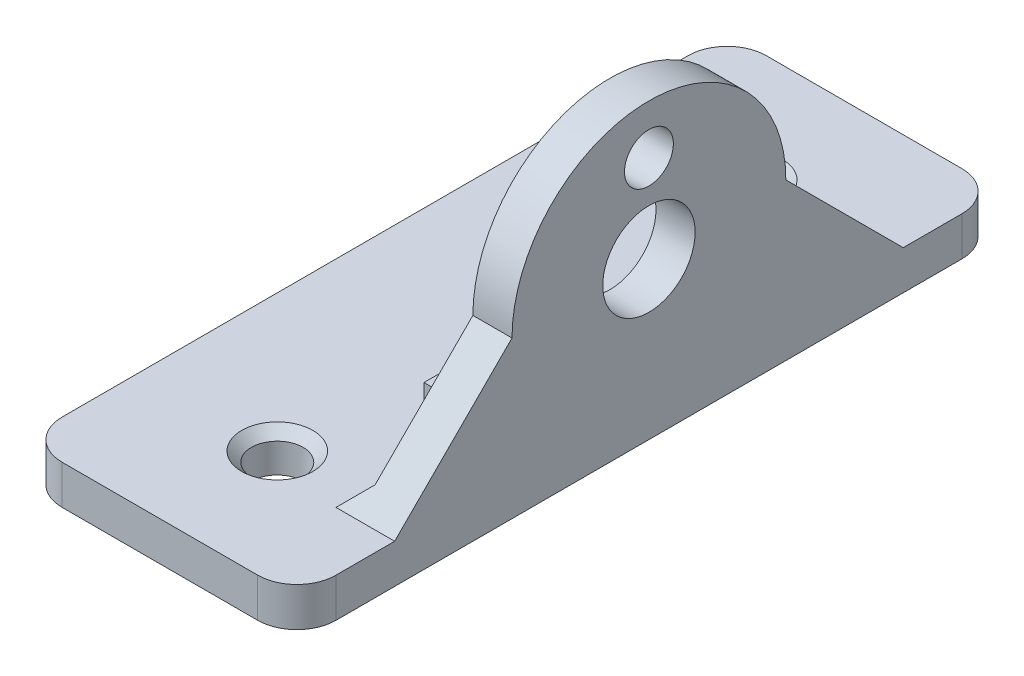
SolidWorks part; units mm, degrees
ref_plane "Front Plane" through (0, 0, 0) normal (0, 0, 1) x (1, 0, 0)
ref_plane "Top Plane" through (0, 0, 0) normal (0, 1, 0) x (1, 0, 0)
ref_plane "Right Plane" through (0, 0, 0) normal (1, 0, 0) x (0, 0, -1)
sketch "Sketch1" plane through (0, 0, 0) normal (1, 0, 0) x (0, 0, -1)
  line L0 (-28.575, 0) -> (28.575, 0)
  line L1 (28.575, 0) -> (28.575, 3.175)
  line L2 (28.575, 3.175) -> (20.6375, 3.175)
  line L3 (-20.6375, 3.175) -> (-28.575, 3.175)
  line L4 (-28.575, 3.175) -> (-28.575, 0)
  line L5 (20.6375, 3.175) -> (11.1125, 12.7)
  line L6 (0, 30.8716) -> (0, -13.4832) construction
  line L7 (-20.6375, 3.175) -> (-11.1125, 12.7)
  arc A0 (11.1125, 12.7) -> (-11.1125, 12.7) centre (0, 12.7) ccw
  circle A1 centre (0, 12.7) radius 3.75
  point P17 (0, 0)
  dimension "D1" = 7.5
  dimension "D2" = 3.175
  dimension "D3" = 11.1125
  dimension "D4" = 12.7
  dimension "D5" = 57.15
  dimension "D6" = 45
extrude "Boss-Extrude1" add sketch "Sketch1" against normal blind 3.175
sketch "Sketch2" plane through (0, 0, 0) normal (1, 0, 0) x (0, 0, -1)
  circle A0 centre (0, 19.812) radius 1.9844
  arc A1 (11.1125, 12.7) -> (-11.1125, 12.7) centre (0, 12.7) ccw construction
  point P5 (0, 0)
  dimension "D1" = 3.9688
  dimension "D2" = 7.112
extrude "Cut-Extrude1" cut sketch "Sketch2" against normal through all
sketch "Sketch3" plane through (-3.175, 0, 0) normal (-1, 0, 0) x (0, 0, 1)
  line L1 (-28.575, 3.175) -> (28.575, 3.175)
  line L2 (-28.575, 3.175) -> (-28.575, 0)
  line L3 (-28.575, 0) -> (28.575, 0)
  line L4 (28.575, 3.175) -> (28.575, 0)
extrude "Boss-Extrude2" add sketch "Sketch3" along normal blind 19.05
sketch "Sketch4" plane through (-3.175, 0, 0) normal (-1, 0, 0) x (0, 0, 1)
  line L1 (7.9375, 5.207) -> (10.3188, 5.207)
  line L2 (7.9375, 5.207) -> (7.9375, 3.175)
  line L3 (7.9375, 3.175) -> (10.3187, 3.175)
  line L4 (10.3188, 5.207) -> (10.3187, 3.175)
  line L5 (28.575, 3.175) -> (-28.575, 3.175) construction
  line L6 (-28.575, 0) -> (28.575, 0) construction
  point P4 (9.5882, 4.6648)
  point P8 (9.8279, 5.2)
  point P9 (7.1781, 5.2)
  point P11 (0, 0)
  dimension "D1" = 2.3812
  dimension "D2" = 2.032
  dimension "D3" = 7.9375
extrude "Boss-Extrude3" add sketch "Sketch4" along normal blind 4.7625
sketch "Sketch5" plane through (0, 3.175, 0) normal (0, 1, 0) x (1, 0, 0)
  line L0 (-22.225, -28.575) -> (0, -28.575) construction
  line L1 (0, 0) -> (-33.4232, 0) construction
  line L2 (0, -11.1125) -> (0, 11.1125) construction
  circle A0 centre (-11.1125, -19.05) radius 2.0955
  circle A1 centre (-11.1125, 19.05) radius 2.0955
  point P4 (-11.1125, -28.575)
  dimension "D1" = 4.191
  dimension "D2" = 9.525
extrude "Cut-Extrude2" cut sketch "Sketch5" against normal through all
chamfer "Chamfer1" distance 0.7937 angle 45 2 edges at (-11.1125, 3.175, 21.1455) (-11.1125, 3.175, -21.1455)
chamfer "Chamfer3" distance 1.5875 angle 45 2 edges at (-3.175, 3.175, -6.35) (-3.175, 3.175, 15.4781)
fillet "Fillet1" radius 3.175 4 edges at (0, 1.5875, -28.575) (-22.225, 1.5875, -28.575) (-22.225, 1.5875, 28.575) (0, 1.5875, 28.575)
